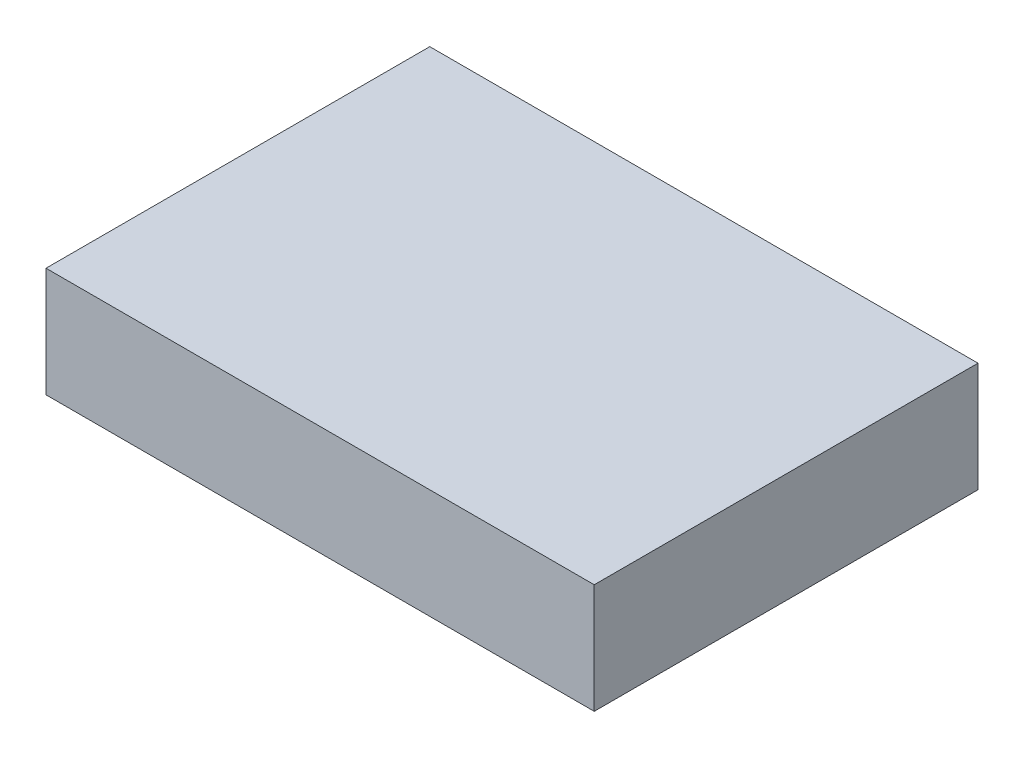
SolidWorks part; units mm, degrees
ref_plane "Front Plane" through (0, 0, 0) normal (0, 0, 1) x (1, 0, 0)
ref_plane "Top Plane" through (0, 0, 0) normal (0, 1, 0) x (1, 0, 0)
ref_plane "Right Plane" through (0, 0, 0) normal (1, 0, 0) x (0, 0, -1)
sketch "Sketch2" plane through (0, 0, 0) normal (0, 1, 0) x (1, 0, 0)
  line L1 (-30.7895, 9.2982) -> (19.2105, 9.2982)
  line L2 (-30.7895, 9.2982) -> (-30.7895, -25.7018)
  line L3 (-30.7895, -25.7018) -> (19.2105, -25.7018)
  line L4 (19.2105, 9.2982) -> (19.2105, -25.7018)
  dimension "D1" = 50
  dimension "D2" = 35
extrude "Boss-Extrude2" add sketch "Sketch2" along normal blind 10
